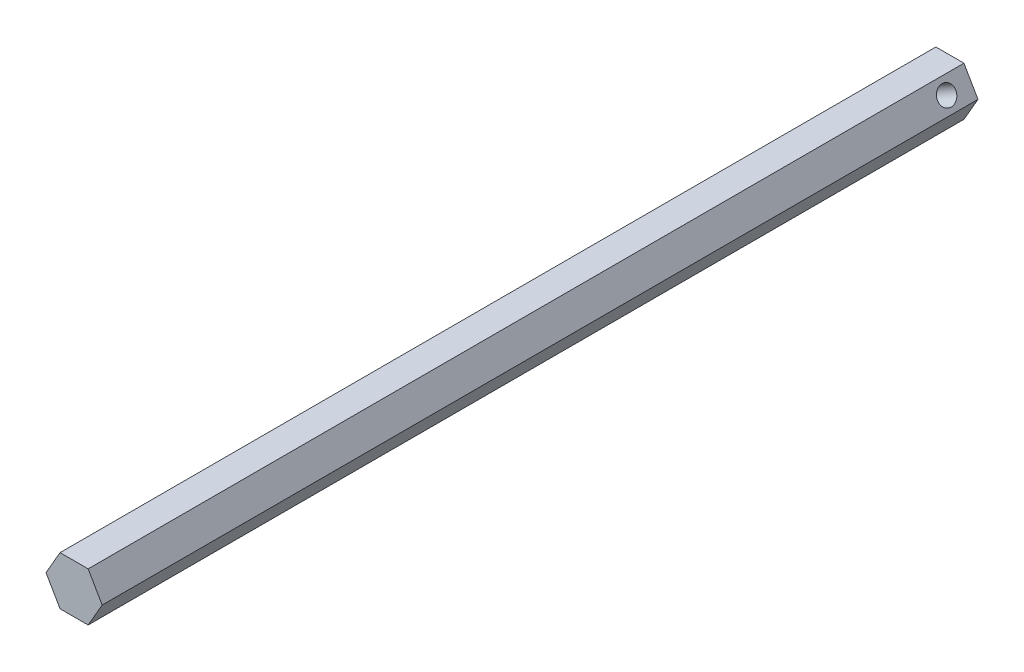
SolidWorks part; units mm, degrees
ref_plane "Front Plane" through (0, 0, 0) normal (0, 0, 1) x (1, 0, 0)
ref_plane "Top Plane" through (0, 0, 0) normal (0, 1, 0) x (1, 0, 0)
ref_plane "Right Plane" through (0, 0, 0) normal (1, 0, 0) x (0, 0, -1)
sketch "Sketch1" plane through (0, 0, 0) normal (0, 0, 1) x (1, 0, 0)
  line L1 (-3.6662, -6.35) -> (3.6662, -6.35)
  line L2 (3.6662, -6.35) -> (7.3323, 0)
  line L3 (7.3323, 0) -> (3.6662, 6.35)
  line L4 (3.6662, 6.35) -> (-3.6662, 6.35)
  line L5 (-3.6662, 6.35) -> (-7.3323, 0)
  line L6 (-7.3323, 0) -> (-3.6662, -6.35)
  circle A0 centre (0, 0) radius 6.35 construction
  point P1 (-3.6662, -6.35)
  dimension "D1" = 12.7
extrude "Boss-Extrude1" add sketch "Sketch1" along normal blind 228.6
sketch "Sketch2" plane through (5.4993, 3.175, 0) normal (0.866, 0.5, 0) x (0, 0, -1)
  line L0 (0, -3.6662) -> (0, 3.6662) construction
  circle A0 centre (-6.35, 0) radius 2.3813
  point P4 (-6.35, 4.8616)
  point P5 (-6.35, 0)
  dimension "D1" = 6.35
  dimension "D2" = 4.7625
extrude "Cut-Extrude1" cut sketch "Sketch2" against normal through all
